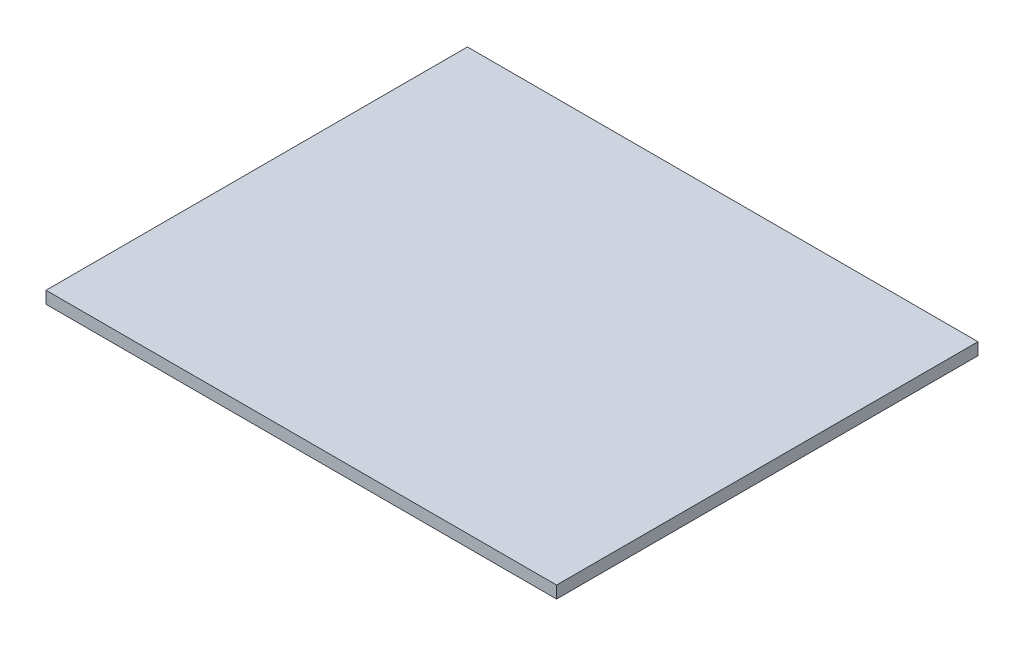
SolidWorks part; units mm, degrees
ref_plane "Front Plane" through (0, 0, 0) normal (0, 0, 1) x (1, 0, 0)
ref_plane "Top Plane" through (0, 0, 0) normal (0, 1, 0) x (1, 0, 0)
ref_plane "Right Plane" through (0, 0, 0) normal (1, 0, 0) x (0, 0, -1)
sketch "Sketch1" plane through (0, 0, 0) normal (0, 1, 0) x (1, 0, 0)
  line L1 (0, 0) -> (200.025, 0)
  line L2 (0, 0) -> (0, -165.1)
  line L3 (0, -165.1) -> (200.025, -165.1)
  line L4 (200.025, 0) -> (200.025, -165.1)
  dimension "D1" = 165.1
  dimension "D2" = 200.025
extrude "Boss-Extrude1" add sketch "Sketch1" along normal blind 4.7625 contours L1 L4 L3 L2
